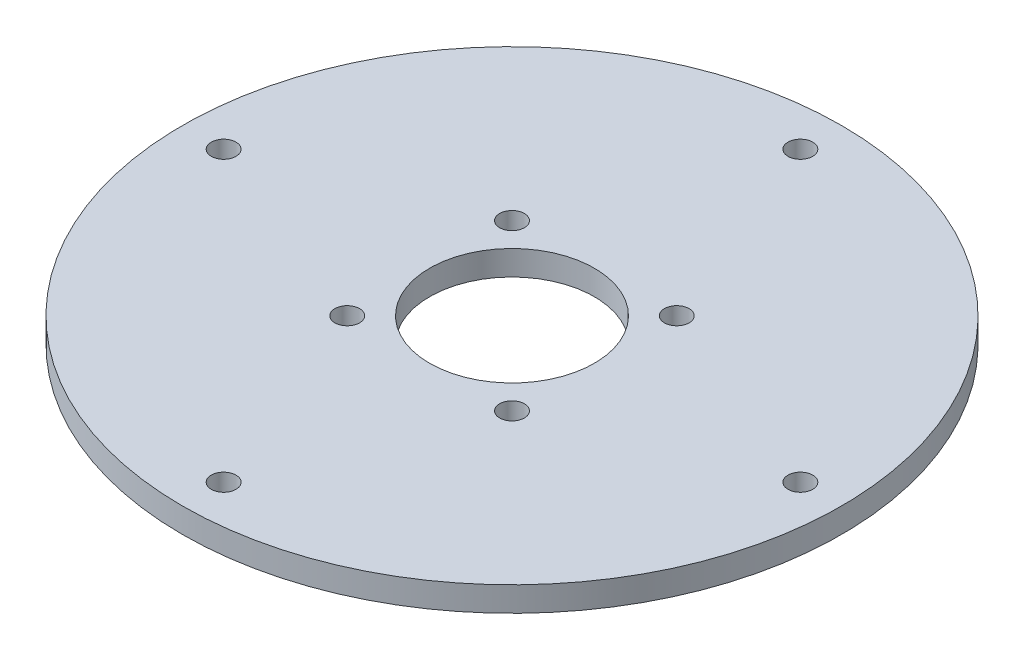
SolidWorks part; units mm, degrees
ref_plane "Front Plane" through (0, 0, 0) normal (0, 0, 1) x (1, 0, 0)
ref_plane "Top Plane" through (0, 0, 0) normal (0, 1, 0) x (1, 0, 0)
ref_plane "Right Plane" through (0, 0, 0) normal (1, 0, 0) x (0, 0, -1)
sketch "Sketch1" plane through (0, 0, 0) normal (0, 1, 0) x (1, 0, 0)
  line L0 (0, 40) -> (0, -40) construction
  line L1 (-40, 0) -> (40, 0) construction
  circle A0 centre (0, 0) radius 40
  circle A1 centre (0, 35) radius 1.5
  circle A2 centre (35, 0) radius 1.5
  circle A3 centre (0, -35) radius 1.5
  circle A4 centre (-35, 0) radius 1.5
  dimension "D1" = 80
  dimension "D2" = 3
  dimension "D3" = 3
  dimension "D4" = 3
  dimension "D5" = 3
  dimension "D6" = 5
  dimension "D7" = 5
  dimension "D8" = 5
  dimension "D9" = 5
extrude "Boss-Extrude1" add sketch "Sketch1" along normal blind 3
sketch "Sketch2" plane through (0, 3, 0) normal (0, 1, 0) x (1, 0, 0)
  line L0 (-10, 10) -> (10, -10) construction
  line L1 (-10, 10) -> (10, 10) construction
  line L2 (-10, 10) -> (-10, -10) construction
  line L3 (-10, -10) -> (10, -10) construction
  line L4 (10, 10) -> (10, -10) construction
  circle A0 centre (10, 10) radius 1.5
  circle A1 centre (-10, 10) radius 1.5
  circle A2 centre (-10, -10) radius 1.5
  circle A3 centre (10, -10) radius 1.5
  point P4 (0, 0)
  dimension "D3" = 3
  dimension "D4" = 3
  dimension "D5" = 3
  dimension "D6" = 3
  dimension "D1" = 20
  dimension "D2" = 20
extrude "Cut-Extrude1" cut sketch "Sketch2" against normal blind 3
sketch "Sketch3" plane through (0, 3, 0) normal (0, 1, 0) x (1, 0, 0)
  circle A0 centre (0, 0) radius 10
  dimension "D1" = 20
extrude "Cut-Extrude2" cut sketch "Sketch3" against normal blind 10
